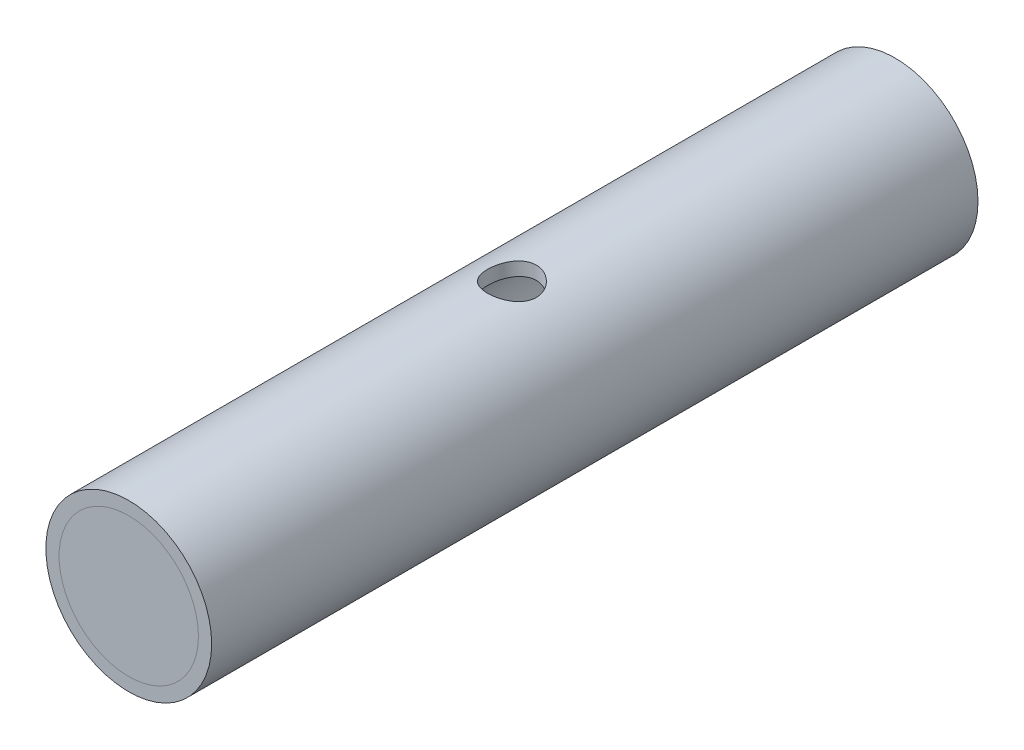
SolidWorks part; units mm, degrees
material "ABS"
ref_plane "Front Plane" through (0, 0, 0) normal (0, 0, 1) x (1, 0, 0)
ref_plane "Top Plane" through (0, 0, 0) normal (0, 1, 0) x (1, 0, 0)
ref_plane "Right Plane" through (0, 0, 0) normal (1, 0, 0) x (0, 0, -1)
sketch "Sketch1" plane through (0, 0, 0) normal (0, 0, 1) x (1, 0, 0)
  circle A0 centre (0, 0) radius 30.226
  circle A1 centre (0, 0) radius 25.4
  dimension "D1" = 60.452
  dimension "D2" = 50.8
extrude "Boss-Extrude1" add sketch "Sketch1" along normal mid plane 279.4
sketch "Sketch2" plane through (0, 0, 0) normal (0, 1, 0) x (1, 0, 0)
  circle A0 centre (0, 0) radius 8.89
  dimension "D1" = 17.78
extrude "Cut-Extrude1" cut sketch "Sketch2" along normal up to surface (30.226 mm away)
surface "Surface-Plane1"
surface "Surface-Plane2"
sketch "Sketch3" plane through (0, 0, 0) normal (0, 1, 0) x (1, 0, 0)
  line L0 (0, -183.9723) -> (0, 183.9723) construction
  point P4 (0, 0)
